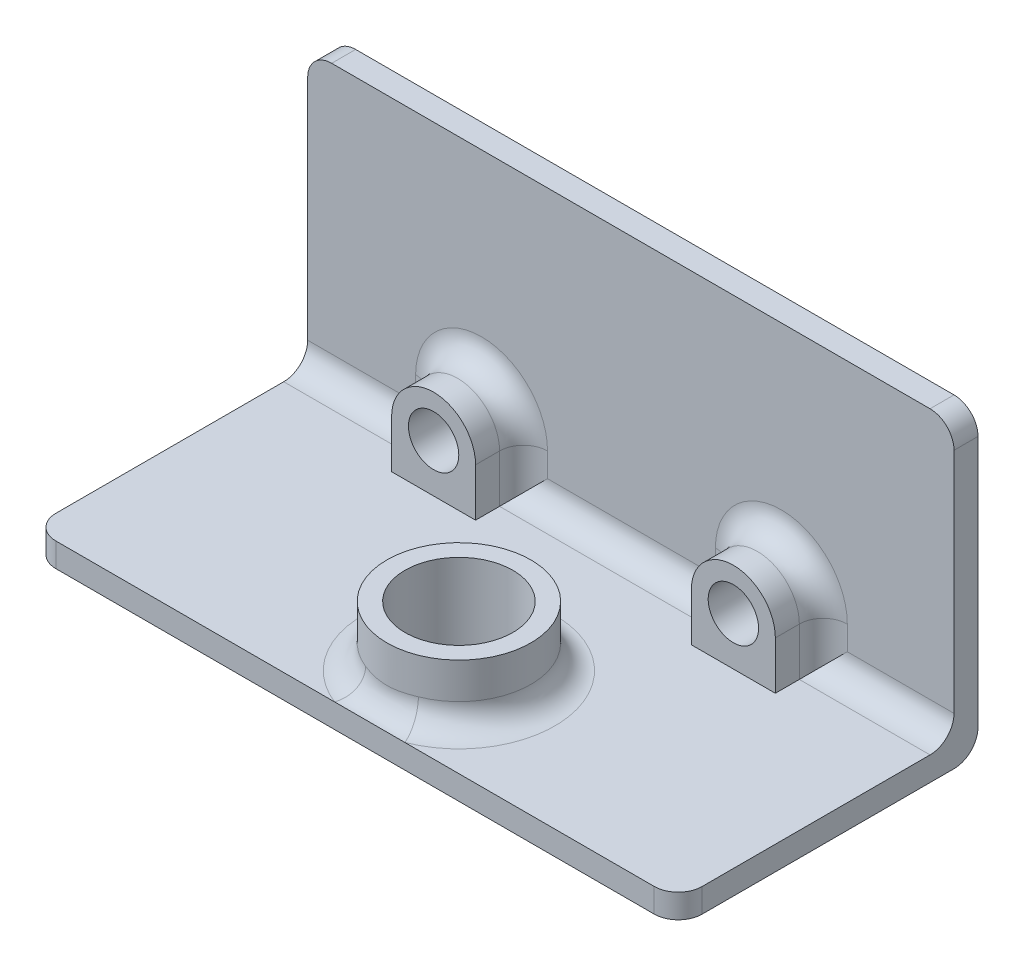
SolidWorks part; units mm, degrees
ref_plane "Front Plane" through (0, 0, 0) normal (0, 0, 1) x (1, 0, 0)
ref_plane "Top Plane" through (0, 0, 0) normal (0, 1, 0) x (1, 0, 0)
ref_plane "Right Plane" through (0, 0, 0) normal (1, 0, 0) x (0, 0, -1)
sketch "Sketch1" plane through (0, 0, 0) normal (0, 0, 1) x (1, 0, 0)
  line L1 (0, 0) -> (53.9, 0)
  line L2 (0, 0) -> (0, 25)
  line L3 (0, 25) -> (53.9, 25)
  line L4 (53.9, 0) -> (53.9, 25)
  line L5 (0, 0) -> (53.9, 25) construction
  line L6 (0, 25) -> (53.9, 0) construction
  point P4 (26.95, 12.5)
  dimension "D1" = 25
  dimension "D2" = 53.9
extrude "Boss-Extrude1" add sketch "Sketch1" along normal blind 2
sketch "Sketch2" plane through (0, 0, 2) normal (0, 0, 1) x (1, 0, 0)
  line L0 (0, 25) -> (0, 0) construction
  line L1 (0, 2) -> (53.9, 2)
  line L2 (0, 2) -> (0, 0)
  line L3 (0, 0) -> (53.9, 0)
  line L4 (53.9, 2) -> (53.9, 0)
  line L5 (0, 2) -> (53.9, 0) construction
  line L6 (0, 0) -> (53.9, 2) construction
  point P4 (26.95, 1)
  dimension "D1" = 2
extrude "Boss-Extrude2" add sketch "Sketch2" along normal blind 23
sketch "Sketch3" plane through (0, 0, 2) normal (0, 0, 1) x (1, 0, 0)
  circle A0 centre (39.5, 6) radius 2.1
  circle A1 centre (14.5, 6) radius 2.1
  dimension "D1" = 4.2
extrude "Cut-Extrude1" cut sketch "Sketch3" against normal through all
sketch "Sketch4" plane through (0, 2, 0) normal (0, 1, 0) x (1, 0, 0)
  line L2 (35.5402, -10.3821) -> (25.1588, -10.3821) construction
  line L3 (53.9, -25) -> (0, -25) construction
  line L4 (34.5179, -24.6402) -> (34.5179, -14.2588) construction
  line L5 (21.2821, -9.3598) -> (21.2821, -19.7412) construction
  circle A0 centre (28.1679, -17.5571) radius 4.5
  dimension "D1" = 9
  dimension "D2" = 7.175
  dimension "D3" = 7.4429
  dimension "D4" = 6.35
  dimension "D5" = 6.8859
extrude "Cut-Extrude2" cut sketch "Sketch4" against normal through all
sketch "Sketch5" plane through (0, 0, 2) normal (0, 0, 1) x (1, 0, 0)
  line L0 (18, 6) -> (18, 2)
  line L1 (53.9, 2) -> (0, 2) construction
  line L2 (18, 2) -> (11, 2)
  line L3 (11, 2) -> (11, 6)
  line L4 (36, 6) -> (36, 2)
  line L5 (36, 2) -> (43, 2)
  line L6 (43, 2) -> (43, 6)
  arc A0 (18, 6) -> (11, 6) centre (14.5, 6) ccw
  arc A1 (43, 6) -> (36, 6) centre (39.5, 6) ccw
  circle A2 centre (14.5, 6) radius 2.1
  circle A3 centre (39.5, 6) radius 2.1
  dimension "D1" = 7
extrude "Boss-Extrude3" add sketch "Sketch5" along normal blind 4
sketch "Sketch6" plane through (0, 2, 0) normal (0, 1, 0) x (1, 0, 0)
  circle A0 centre (28.1679, -17.5571) radius 6
  circle A1 centre (28.1679, -17.5571) radius 4.5
  dimension "D1" = 9
  dimension "D2" = 12
extrude "Boss-Extrude4" add sketch "Sketch6" along normal blind 5
fillet "Fillet1" radius 2 15 edges at (43, 4, 2) (39.5, 9.5, 2) (18, 4, 2) (14.5, 9.5, 2) (26.95, 0, 0) (53.9, 1, 25) (0, 1, 25) (0, 25, 1) (53.9, 25, 1) (48.45, 2, 2) (5.5, 2, 2) (27, 2, 2) (36, 4, 2) (11, 4, 2) (34.1679, 2, 17.5571)
